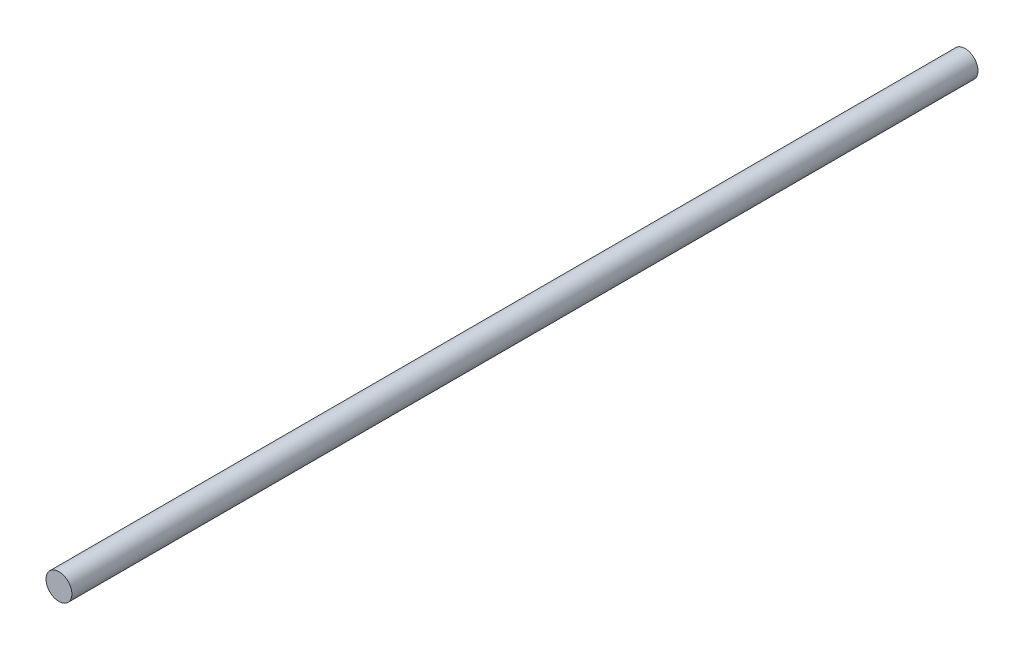
SolidWorks part; units mm, degrees
material "Carbon Fibre"
ref_plane "Front Plane" through (0, 0, 0) normal (0, 0, 1) x (1, 0, 0)
ref_plane "Top Plane" through (0, 0, 0) normal (0, 1, 0) x (1, 0, 0)
ref_plane "Right Plane" through (0, 0, 0) normal (1, 0, 0) x (0, 0, -1)
sketch "Sketch1" plane through (0, 0, 0) normal (0, 0, 1) x (1, 0, 0)
  circle A0 centre (0, 0) radius 6.35
  dimension "D1" = 12.7
extrude "Boss-Extrude1" add sketch "Sketch1" along normal blind 444.5
